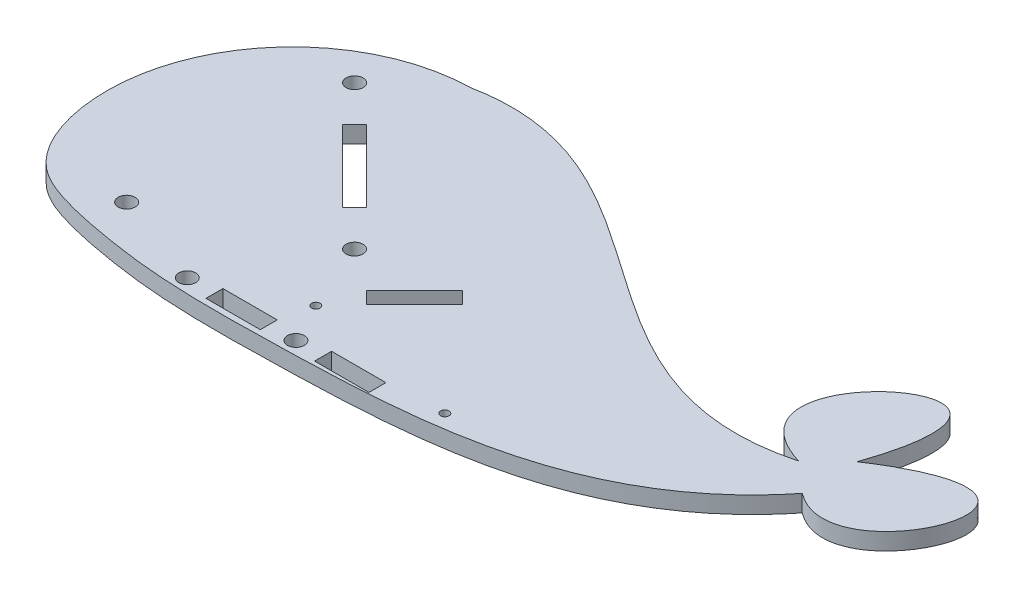
SolidWorks part; units mm, degrees
ref_plane "Front Plane" through (0, 0, 0) normal (0, 0, 1) x (1, 0, 0)
ref_plane "Top Plane" through (0, 0, 0) normal (0, 1, 0) x (1, 0, 0)
ref_plane "Right Plane" through (0, 0, 0) normal (1, 0, 0) x (0, 0, -1)
sketch "Sketch2" plane through (0, 0, 0) normal (0, 1, 0) x (1, 0, 0)
  line L0 (53.3333, 94.5) -> (266.6667, 94.5) construction
  line L1 (0, 0) -> (152.4, 0) construction
  line L2 (0, 0) -> (0, 90.0113) construction
  line L3 (0, 90.0113) -> (152.4, 90.0113) construction
  line L4 (152.4, 0) -> (152.4, 90.0113) construction
  line L5 (20.4472, 56.5141) -> (23.1413, 53.82) construction
  line L6 (20.6717, 54.0445) -> (22.9168, 56.2896) construction
  line L7 (49.8575, 29.3488) -> (47.6125, 27.1037) construction
  line L8 (47.388, 29.5733) -> (50.082, 26.8792) construction
  line L9 (27.4069, 47.3093) -> (40.8773, 33.8389)
  line L10 (40.8773, 33.8389) -> (43.1223, 36.084)
  line L11 (43.1223, 36.084) -> (29.6519, 49.5544)
  line L12 (29.6519, 49.5544) -> (27.4069, 47.3093)
  line L13 (27.4069, 47.3093) -> (40.8773, 33.8389)
  line L14 (40.8773, 33.8389) -> (43.1223, 36.084)
  line L15 (43.1223, 36.084) -> (29.6519, 49.5544)
  line L16 (29.6519, 49.5544) -> (27.4069, 47.3093)
  line L17 (58.8378, 20.3685) -> (67.818, 29.3488)
  line L18 (67.818, 29.3488) -> (65.573, 31.5938)
  line L19 (65.573, 31.5938) -> (56.5927, 22.6136)
  line L20 (56.5927, 22.6136) -> (58.8378, 20.3685)
  line L21 (58.8378, 20.3685) -> (67.818, 29.3488)
  line L22 (67.818, 29.3488) -> (65.573, 31.5938)
  line L23 (65.573, 31.5938) -> (56.5927, 22.6136)
  line L24 (56.5927, 22.6136) -> (58.8378, 20.3685)
  line L25 (19.3247, 55.3915) -> (22.0187, 52.6975)
  line L26 (22.0187, 52.6975) -> (24.2638, 54.9425)
  line L27 (24.2638, 54.9425) -> (21.5697, 57.6366)
  line L28 (21.5697, 57.6366) -> (19.3247, 55.3915)
  line L29 (19.3247, 55.3915) -> (22.0187, 52.6975) construction
  line L30 (22.0187, 52.6975) -> (24.2638, 54.9425) construction
  line L31 (24.2638, 54.9425) -> (21.5697, 57.6366) construction
  line L32 (21.5697, 57.6366) -> (19.3247, 55.3915) construction
  line L33 (46.2654, 28.4508) -> (48.9595, 25.7567)
  line L34 (48.9595, 25.7567) -> (51.2046, 28.0017)
  line L35 (51.2046, 28.0017) -> (48.5105, 30.6958)
  line L36 (48.5105, 30.6958) -> (46.2654, 28.4508)
  line L37 (46.2654, 28.4508) -> (48.9595, 25.7567) construction
  line L38 (48.9595, 25.7567) -> (51.2046, 28.0017) construction
  line L39 (51.2046, 28.0017) -> (48.5105, 30.6958) construction
  line L40 (48.5105, 30.6958) -> (46.2654, 28.4508) construction
  circle A0 centre (54.2708, 15.4375) radius 0.7937
  circle A1 centre (83.7808, 10.0573) radius 0.7937 construction
  circle A2 centre (83.7808, 10.0573) radius 0.7937
  circle A3 centre (21.7942, 55.167) radius 1.5875
  circle A4 centre (48.735, 28.2263) radius 1.5875
  circle A5 centre (19.821, 14.5195) radius 1.5875 construction
  circle A6 centre (19.821, 14.5195) radius 1.5875
  spline S0 degree 3 poles (33.497, 65.2328) (13.8358, 64.7768) (-6.4098, 41.7343) (3.6225, 12.8066) (14.4019, 8.7512) (21.8663, 7.2089) (35.9768, 4.9995) (73.9872, 5.5366) (111.7144, 7.4474) (130.1591, 30.5277) knots 0 0 0 0 0.267337 0.357506 0.391567 0.432957 0.471434 0.602901 1 1 1 1
  spline S1 degree 3 poles (33.497, 65.2328) (68.1711, 72.0943) (87.4426, 25.5099) (124.569, 35.419) knots 0 0 0 0 1 1 1 1
  spline S2 degree 3 poles (124.569, 35.419) (97.9718, 43.7536) (143.3997, 78.8879) (130.1591, 40.7762) knots 0 0 0 0 1 1 1 1
  spline S3 degree 3 poles (130.1591, 30.5277) (146.2156, 18.4305) (163.0669, 62.486) (130.1591, 40.7762) knots 0 0 0 0 1 1 1 1
  dimension "D3" = 1.5875
  dimension "D8" = 3.175
  dimension "D9" = 3.175
  dimension "D1" = 90.0113
  dimension "D2" = 152.4
  dimension "D4" = 0
  dimension "D5" = 0
  dimension "D6" = 0
  dimension "D7" = 0
extrude "Boss-Extrude1" add sketch "Sketch2" along normal blind 3.175
sketch "Sketch6" plane through (0, 3.175, 0) normal (0, 1, 0) x (1, 0, 0)
  line L0 (37.7316, 9.5284) -> (37.7316, 6.3534) construction
  line L1 (27.5716, 9.5284) -> (32.6516, 9.5284)
  line L2 (27.5716, 9.5284) -> (27.5716, 6.3534)
  line L3 (27.5716, 6.3534) -> (32.6516, 6.3534)
  line L4 (32.6516, 9.5284) -> (32.6516, 6.3534)
  line L5 (32.6516, 9.5284) -> (42.8116, 9.5284)
  line L6 (32.6516, 9.5284) -> (32.6516, 6.3534)
  line L7 (32.6516, 6.3534) -> (42.8116, 6.3534)
  line L8 (42.8116, 9.5284) -> (42.8116, 6.3534)
  line L9 (42.8116, 9.5284) -> (52.9716, 9.5284)
  line L10 (42.8116, 9.5284) -> (42.8116, 6.3534)
  line L11 (42.8116, 6.3534) -> (52.9716, 6.3534)
  line L12 (52.9716, 9.5284) -> (52.9716, 6.3534)
  line L13 (52.9716, 9.5284) -> (63.1316, 9.5284)
  line L14 (52.9716, 9.5284) -> (52.9716, 6.3534)
  line L15 (52.9716, 6.3534) -> (63.1316, 6.3534)
  line L16 (63.1316, 9.5284) -> (63.1316, 6.3534)
  line L17 (63.1316, 9.5284) -> (73.2916, 9.5284)
  line L18 (63.1316, 9.5284) -> (63.1316, 6.3534)
  line L19 (63.1316, 6.3534) -> (73.2916, 6.3534)
  line L20 (73.2916, 9.5284) -> (73.2916, 6.3534)
  line L21 (73.2916, 9.5284) -> (78.3716, 9.5284)
  line L22 (73.2916, 9.5284) -> (73.2916, 6.3534)
  line L23 (73.2916, 6.3534) -> (78.3716, 6.3534)
  line L24 (78.3716, 9.5284) -> (78.3716, 6.3534)
  line L25 (58.0516, 9.5284) -> (58.0516, 6.3534) construction
  line L26 (32.6516, 7.9409) -> (42.8116, 7.9409) construction
  line L27 (52.9716, 7.9409) -> (63.1316, 7.9409) construction
  circle A0 centre (37.7316, 7.9409) radius 1.5875
  circle A1 centre (58.0516, 7.9409) radius 1.5875
  dimension "D1" = 3.175
  dimension "D2" = 3.175
  dimension "D3" = 10.16
  dimension "D4" = 10.16
  dimension "D5" = 10.16
extrude "Cut-Extrude7" cut sketch "Sketch6" against normal blind 3.175 contours A0 | L12 L9 L8 L11 | A1 | L20 L17 L16 L19
